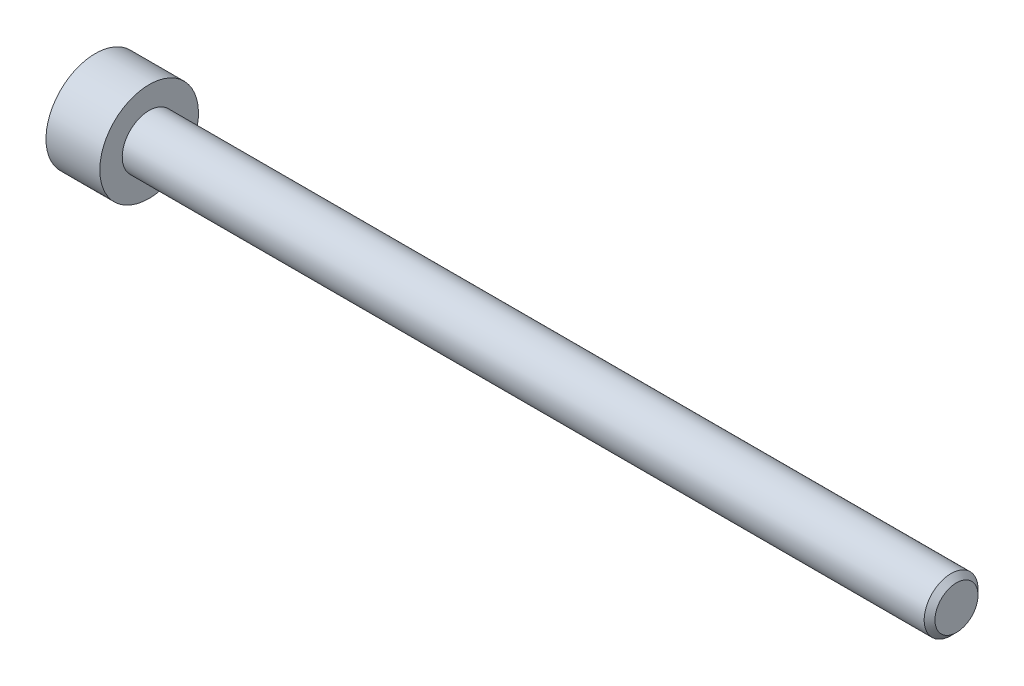
SolidWorks part; units mm, degrees
material "Plain Carbon Steel"
ref_plane "Front Plane" through (0, 0, 0) normal (0, 0, 1) x (1, 0, 0)
ref_plane "Top Plane" through (0, 0, 0) normal (0, 1, 0) x (1, 0, 0)
ref_plane "Right Plane" through (0, 0, 0) normal (1, 0, 0) x (0, 0, -1)
sketch "Sketch2" plane through (0, 0, 0) normal (1, 0, 0) x (0, 0, -1)
  circle A0 centre (0, 0) radius 1.5
  dimension "D1" = 3
extrude "Boss-Extrude1" add sketch "Sketch2" against normal blind 45
chamfer "Chamfer1" distance 0.3 angle 45 1 edges at (0, 0, -1.5)
sketch "Sketch6" plane through (0, 0, 0) normal (0, 0, 1) x (1, 0, 0)
  line L0 (-48, 0) -> (-48, 2.75)
  line L1 (-48, 0) -> (-45, 0)
  line L2 (-48, 2.75) -> (-45, 2.75)
  line L6 (-45, 2.75) -> (-45, 0)
  line L8 (-45, 0) -> (-14.6471, 0) construction
  line L10 (-45, 1.5) -> (-45, -1.5) construction
  dimension "D1" = 3
  dimension "D2" = 5.5
revolve "Revolve1" add sketch "Sketch6" angle 360 about L8
sketch "Sketch7" plane through (-48, 0, 0) normal (-1, 0, 0) x (0, 0, 1)
  line L1 (0, 1.4434) -> (-1.25, 0.7217)
  line L2 (-1.25, 0.7217) -> (-1.25, -0.7217)
  line L3 (-1.25, -0.7217) -> (0, -1.4434)
  line L4 (0, -1.4434) -> (1.25, -0.7217)
  line L5 (1.25, -0.7217) -> (1.25, 0.7217)
  line L6 (1.25, 0.7217) -> (0, 1.4434)
  circle A0 centre (0, 0) radius 1.25 construction
  dimension "D1" = 2.5
extrude "Cut-Extrude1" cut sketch "Sketch7" against normal blind 1.6
sketch "Sketch8" plane through (-48, 0, 0) normal (-1, 0, 0) x (0, 0, 1)
  circle A0 centre (0, 0) radius 1.4934
  dimension "D1" = 0.05
extrude "Cut-Extrude2" cut sketch "Sketch8" against normal blind 1 draft 45
